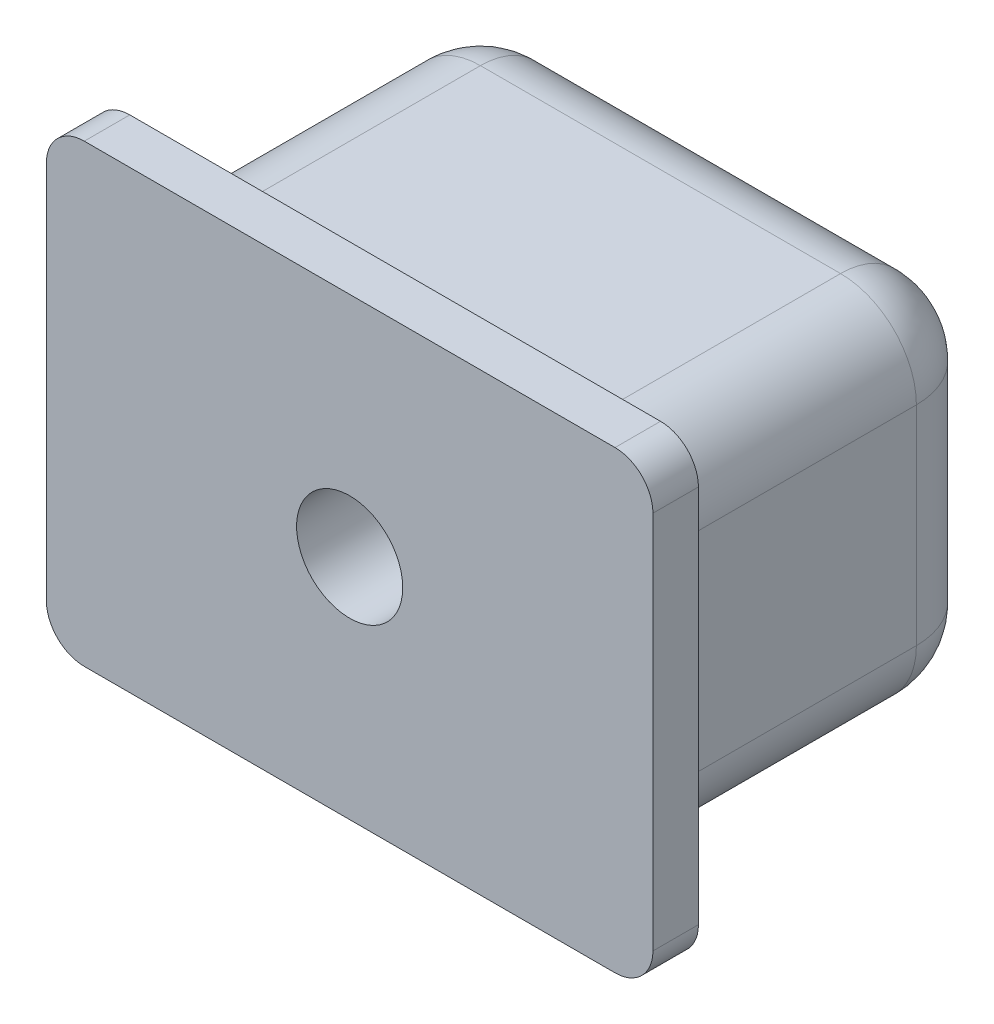
SolidWorks part; units mm, degrees
ref_plane "Front Plane" through (0, 0, 0) normal (0, 0, 1) x (1, 0, 0)
ref_plane "Top Plane" through (0, 0, 0) normal (0, 1, 0) x (1, 0, 0)
ref_plane "Right Plane" through (0, 0, 0) normal (1, 0, 0) x (0, 0, -1)
sketch "Sketch1" plane through (0, 0, 0) normal (0, 0, 1) x (1, 0, 0)
  line L1 (-6.75, -4.75) -> (6.75, -4.75)
  line L2 (-6.75, -4.75) -> (-6.75, 4.75)
  line L3 (-6.75, 4.75) -> (6.75, 4.75)
  line L4 (6.75, -4.75) -> (6.75, 4.75)
  line L5 (-6.75, -4.75) -> (6.75, 4.75) construction
  line L6 (-6.75, 4.75) -> (6.75, -4.75) construction
  point P0 (0, 0)
  dimension "D1" = 13.5
  dimension "D2" = 9.5
extrude "Boss-Extrude1" add sketch "Sketch1" along normal blind 9
sketch "Sketch2" plane through (0, 0, 9) normal (0, 0, 1) x (1, 0, 0)
  line L1 (-8, -6) -> (8, -6)
  line L2 (-8, -6) -> (-8, 6)
  line L3 (-8, 6) -> (8, 6)
  line L4 (8, -6) -> (8, 6)
  line L5 (-8, -6) -> (8, 6) construction
  line L6 (-8, 6) -> (8, -6) construction
  point P1 (0, 0)
  dimension "D1" = 16
  dimension "D2" = 12
extrude "Boss-Extrude2" add sketch "Sketch2" along normal blind 1.2
sketch "Sketch3" plane through (0, 0, 10.2) normal (0, 0, 1) x (1, 0, 0)
  circle A0 centre (0, 0) radius 1.4
  dimension "D1" = 2.8
extrude "Cut-Extrude1" cut sketch "Sketch3" against normal blind 5
fillet "Fillet1" radius 2 4 edges at (-6.75, -4.75, 4.5) (6.75, -4.75, 4.5) (6.75, 4.75, 4.5) (-6.75, 4.75, 4.5)
fillet "Fillet2" radius 2 8 edges at (6.1642, 4.1642, 0) (6.75, 0, 0) (6.1642, -4.1642, 0) (0, -4.75, 0) (-6.1642, -4.1642, 0) (-6.75, 0, 0) (-6.1642, 4.1642, 0) (0, 4.75, 0)
fillet "Fillet3" radius 0.4 8 edges at (6.1642, 4.1642, 9) (6.75, 0, 9) (6.1642, -4.1642, 9) (0, -4.75, 9) (-6.1642, -4.1642, 9) (-6.75, 0, 9) (-6.1642, 4.1642, 9) (0, 4.75, 9)
fillet "Fillet4" radius 1 4 edges at (8, 6, 9.6) (8, -6, 9.6) (-8, -6, 9.6) (-8, 6, 9.6)
